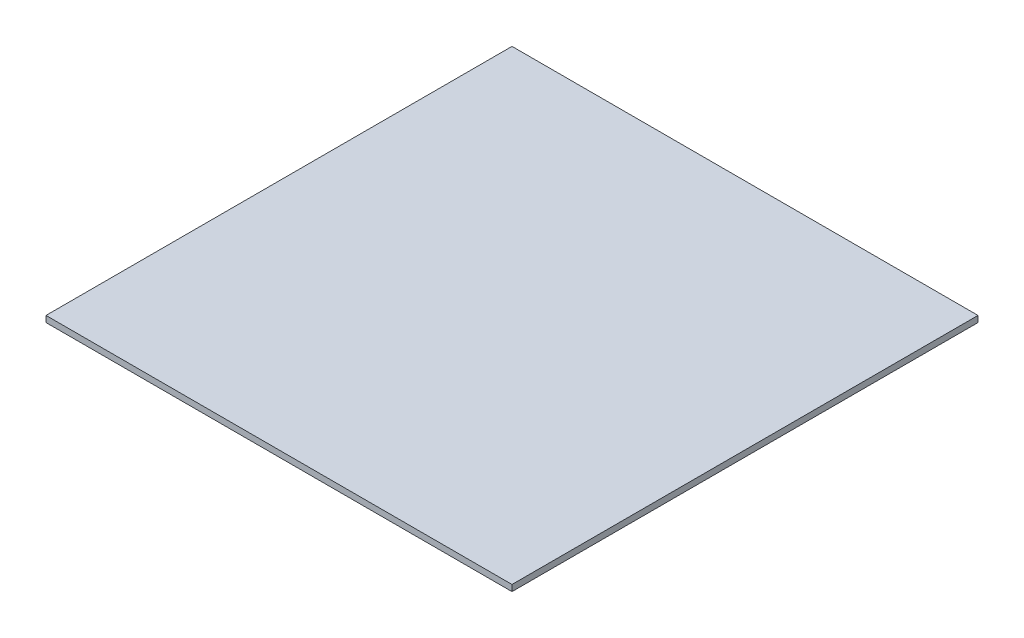
SolidWorks part; units mm, degrees
ref_plane "Plan de face" through (0, 0, 0) normal (0, 0, 1) x (1, 0, 0)
ref_plane "Plan de dessus" through (0, 0, 0) normal (0, 1, 0) x (1, 0, 0)
ref_plane "Plan de droite" through (0, 0, 0) normal (1, 0, 0) x (0, 0, -1)
sketch "Esquisse1" plane through (0, 0, 0) normal (0, 1, 0) x (1, 0, 0)
  line L1 (-75, 75) -> (75, 75)
  line L2 (-75, 75) -> (-75, -75)
  line L3 (-75, -75) -> (75, -75)
  line L4 (75, 75) -> (75, -75)
  dimension "D1" = 150
  dimension "D2" = 150
  dimension "D3" = 75
  dimension "D4" = 75
extrude "Boss.-Extru.1" add sketch "Esquisse1" along normal blind 2
sketch "Esquisse2" plane through (0, 2, 0) normal (0, 1, 0) x (1, 0, 0)
  circle A0 centre (0, 0) radius 13
  dimension "D1" = 26
equation "\"D3@Esquisse1\"=\"D2@Esquisse1\"/2"
equation "\"D4@Esquisse1\"=\"D1@Esquisse1\"/2"
